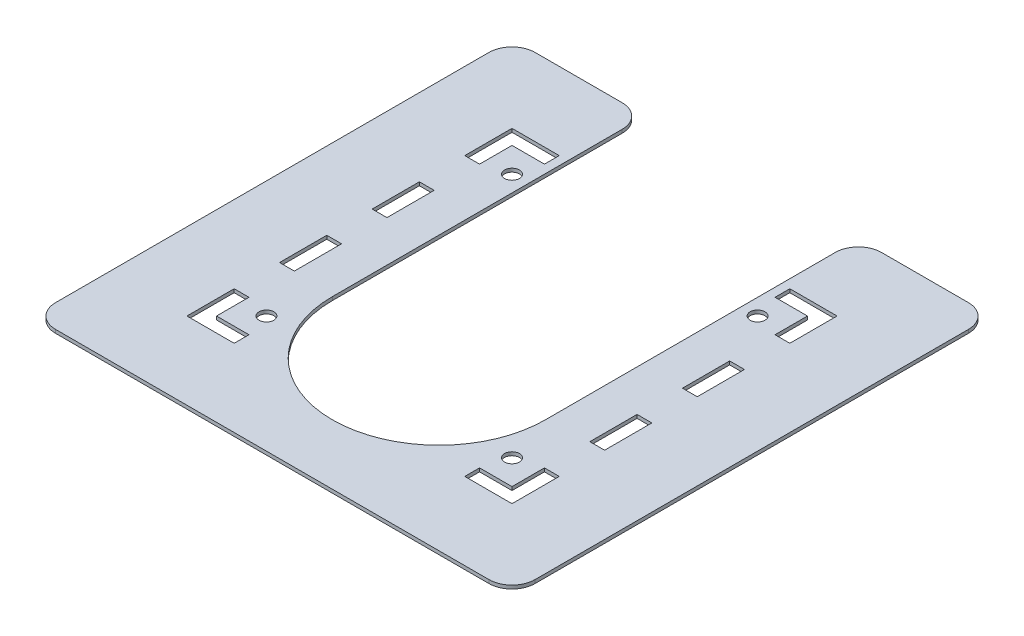
SolidWorks part; units mm, degrees
ref_plane "Front Plane" through (0, 0, 0) normal (0, 0, 1) x (1, 0, 0)
ref_plane "Top Plane" through (0, 0, 0) normal (0, 1, 0) x (1, 0, 0)
ref_plane "Right Plane" through (0, 0, 0) normal (1, 0, 0) x (0, 0, -1)
sketch "Sketch1" plane through (0, 0, 0) normal (0, 1, 0) x (1, 0, 0)
  line L0 (0, 0) -> (0, 21) construction
  line L1 (51.8722, -39.9014) -> (51.8722, 63.843) construction
  line L3 (51.8722, 63.843) -> (-51.8722, 63.843) construction
  line L4 (-51.8722, 63.843) -> (-51.8722, -39.9014) construction
  line L5 (51.8722, -34.9014) -> (51.8722, 58.843)
  line L6 (-46.8722, -39.9014) -> (46.8722, -39.9014)
  line L7 (51.8722, 63.843) -> (-51.8722, 63.843) construction
  line L8 (-51.8722, 58.843) -> (-51.8722, -34.9014)
  line L10 (36.8722, -39.9014) -> (36.8722, 63.843) construction
  line L11 (-36.8722, -39.9014) -> (-36.8722, 63.843) construction
  line L12 (36.8722, -39.9014) -> (36.8722, 63.843) construction
  line L13 (-36.8722, -39.9014) -> (-36.8722, 63.843) construction
  line L14 (23.0585, -3.843) -> (23.0585, 58.843)
  line L15 (-23.0585, -3.843) -> (-23.0585, 58.843)
  line L16 (-46.8722, 63.843) -> (-28.0585, 63.843)
  line L17 (28.0585, 63.843) -> (46.8722, 63.843)
  circle A0 centre (0, 0) radius 21 construction
  circle A1 centre (0, 0) radius 21 construction
  circle A2 centre (26.5585, -14.5877) radius 1.6 construction
  circle A3 centre (-26.5585, -14.5877) radius 1.6 construction
  circle A4 centre (26.5585, 38.5292) radius 1.6 construction
  circle A5 centre (-26.5585, 38.5292) radius 1.6 construction
  circle A6 centre (26.5585, -14.5877) radius 1.6
  circle A7 centre (-26.5585, -14.5877) radius 1.6
  circle A8 centre (26.5585, 38.5292) radius 1.6
  circle A9 centre (-26.5585, 38.5292) radius 1.6
  circle A10 centre (0, -3.843) radius 21.0585 construction
  arc A11 (-21.0585, -3.843) -> (21.0585, -3.843) centre (0, -3.843) ccw construction
  arc A12 (-23.0585, -3.843) -> (23.0585, -3.843) centre (0, -3.843) ccw
  arc A13 (28.0585, 63.843) -> (23.0585, 58.843) centre (28.0585, 58.843) ccw
  circle A14 centre (0, -3.843) radius 23.0585 construction
  arc A15 (-28.0585, 63.843) -> (-23.0585, 58.843) centre (-28.0585, 58.843) cw
  arc A16 (46.8722, 63.843) -> (51.8722, 58.843) centre (46.8722, 58.843) cw
  arc A17 (51.8722, -34.9014) -> (46.8722, -39.9014) centre (46.8722, -34.9014) cw
  arc A18 (-46.8722, -39.9014) -> (-51.8722, -34.9014) centre (-46.8722, -34.9014) cw
  arc A19 (-51.8722, 58.843) -> (-46.8722, 63.843) centre (-46.8722, 58.843) cw
  point P39 (31.0585, -3.843)
  point P42 (23.0585, 63.843)
  point P45 (-23.0585, 63.843)
  dimension "D1" = 2
  dimension "D2" = 5
sketch "Sketch2" plane through (0, 0, 0) normal (0, 0, 1) x (1, 0, 0)
  line L1 (51.8722, -0.75) -> (-51.8722, -0.75)
  line L2 (51.8722, -0.75) -> (51.8722, 0)
  line L3 (51.8722, 0) -> (-51.8722, 0)
  line L4 (-51.8722, -0.75) -> (-51.8722, 0)
extrude "Boss-Extrude1" add sketch "Sketch1" against normal up to vertex (0.75 mm away) up to point (51.8722, -0.75, 0)
sketch "Sketch3" plane through (0, 0, 0) normal (0, 1, 0) x (1, 0, 0)
  line L4 (31.9585, -3.1543) -> (35.1585, -3.1543)
  line L5 (31.9585, 7.0624) -> (31.9585, -3.1543)
  line L6 (35.1585, 7.0624) -> (31.9585, 7.0624)
  line L7 (35.1585, -3.1543) -> (35.1585, 7.0624)
  line L8 (31.9585, -3.1543) -> (35.1585, -3.1543)
  line L9 (31.9585, 7.0624) -> (31.9585, -3.1543)
  line L10 (35.1585, 7.0624) -> (31.9585, 7.0624)
  line L11 (35.1585, -3.1543) -> (35.1585, 7.0624)
  line L12 (35.1585, 16.8791) -> (35.1585, 27.0958)
  line L13 (31.9585, 16.8791) -> (35.1585, 16.8791)
  line L14 (35.1585, 36.9125) -> (35.1585, 47.1292)
  line L15 (35.1585, 47.1292) -> (24.9418, 47.1292)
  line L16 (24.9418, 47.1292) -> (24.9418, 43.9292)
  line L17 (24.9418, 43.9292) -> (31.9585, 43.9292)
  line L18 (31.9585, 43.9292) -> (31.9585, 36.9125)
  line L19 (31.9585, 36.9125) -> (35.1585, 36.9125)
  line L20 (35.1585, 36.9125) -> (35.1585, 47.1292)
  line L21 (35.1585, 47.1292) -> (24.9418, 47.1292)
  line L22 (24.9418, 47.1292) -> (24.9418, 43.9292)
  line L23 (24.9418, 43.9292) -> (31.9585, 43.9292)
  line L24 (31.9585, 43.9292) -> (31.9585, 36.9125)
  line L25 (31.9585, 36.9125) -> (35.1585, 36.9125)
  line L26 (31.9585, 27.0958) -> (31.9585, 16.8791)
  line L27 (35.1585, 27.0958) -> (31.9585, 27.0958)
  line L28 (35.1585, 16.8791) -> (35.1585, 27.0958)
  line L29 (31.9585, 16.8791) -> (35.1585, 16.8791)
  line L30 (31.9585, 27.0958) -> (31.9585, 16.8791)
  line L31 (35.1585, 27.0958) -> (31.9585, 27.0958)
  line L32 (-35.1585, 27.0958) -> (-35.1585, 16.8791)
  line L33 (-35.1585, 16.8791) -> (-31.9585, 16.8791)
  line L34 (-31.9585, 16.8791) -> (-31.9585, 27.0958)
  line L35 (-31.9585, 27.0958) -> (-35.1585, 27.0958)
  line L36 (-35.1585, 27.0958) -> (-35.1585, 16.8791)
  line L37 (-35.1585, 16.8791) -> (-31.9585, 16.8791)
  line L38 (-31.9585, 16.8791) -> (-31.9585, 27.0958)
  line L39 (-31.9585, 27.0958) -> (-35.1585, 27.0958)
  line L40 (-31.9585, 7.0624) -> (-35.1585, 7.0624)
  line L41 (-35.1585, 7.0624) -> (-35.1585, -3.1543)
  line L42 (-31.9585, 36.9125) -> (-31.9585, 43.9292)
  line L43 (-35.1585, 36.9125) -> (-31.9585, 36.9125)
  line L44 (-35.1585, 47.1292) -> (-35.1585, 36.9125)
  line L45 (-24.9418, 47.1292) -> (-35.1585, 47.1292)
  line L46 (-24.9418, 43.9292) -> (-24.9418, 47.1292)
  line L47 (-31.9585, 43.9292) -> (-24.9418, 43.9292)
  line L48 (-31.9585, 36.9125) -> (-31.9585, 43.9292)
  line L49 (-35.1585, 36.9125) -> (-31.9585, 36.9125)
  line L50 (-35.1585, 47.1292) -> (-35.1585, 36.9125)
  line L51 (-24.9418, 47.1292) -> (-35.1585, 47.1292)
  line L52 (-24.9418, 43.9292) -> (-24.9418, 47.1292)
  line L53 (-31.9585, 43.9292) -> (-24.9418, 43.9292)
  line L54 (31.9585, -12.971) -> (31.9585, -19.9877)
  line L55 (35.1585, -12.971) -> (31.9585, -12.971)
  line L56 (35.1585, -23.1877) -> (35.1585, -12.971)
  line L57 (24.9418, -23.1877) -> (35.1585, -23.1877)
  line L58 (24.9418, -19.9877) -> (24.9418, -23.1877)
  line L59 (31.9585, -19.9877) -> (24.9418, -19.9877)
  line L60 (31.9585, -12.971) -> (31.9585, -19.9877)
  line L61 (35.1585, -12.971) -> (31.9585, -12.971)
  line L62 (35.1585, -23.1877) -> (35.1585, -12.971)
  line L63 (24.9418, -23.1877) -> (35.1585, -23.1877)
  line L64 (24.9418, -19.9877) -> (24.9418, -23.1877)
  line L65 (31.9585, -19.9877) -> (24.9418, -19.9877)
  line L66 (-35.1585, -12.971) -> (-35.1585, -23.1877)
  line L67 (-35.1585, -23.1877) -> (-24.9418, -23.1877)
  line L68 (-24.9418, -23.1877) -> (-24.9418, -19.9877)
  line L69 (-24.9418, -19.9877) -> (-31.9585, -19.9877)
  line L70 (-31.9585, -19.9877) -> (-31.9585, -12.971)
  line L71 (-31.9585, -12.971) -> (-35.1585, -12.971)
  line L72 (-35.1585, -12.971) -> (-35.1585, -23.1877)
  line L73 (-35.1585, -23.1877) -> (-24.9418, -23.1877)
  line L74 (-24.9418, -23.1877) -> (-24.9418, -19.9877)
  line L75 (-24.9418, -19.9877) -> (-31.9585, -19.9877)
  line L76 (-31.9585, -19.9877) -> (-31.9585, -12.971)
  line L77 (-31.9585, -12.971) -> (-35.1585, -12.971)
  line L78 (-35.1585, -3.1543) -> (-31.9585, -3.1543)
  line L79 (-31.9585, -3.1543) -> (-31.9585, 7.0624)
  line L80 (-31.9585, 7.0624) -> (-35.1585, 7.0624)
  line L81 (-35.1585, 7.0624) -> (-35.1585, -3.1543)
  line L82 (-35.1585, -3.1543) -> (-31.9585, -3.1543)
  line L83 (-31.9585, -3.1543) -> (-31.9585, 7.0624)
  dimension "D1" = 0
  dimension "D2" = 0
  dimension "D3" = 0
  dimension "D4" = 0
  dimension "D5" = 0
  dimension "D6" = 0
  dimension "D7" = 0
  dimension "D8" = 0
extrude "Cut-Extrude1" cut sketch "Sketch3" against normal through all
sketch "Sketch4" [suppressed] plane through (0, 0, 0) normal (0, 1, 0) x (1, 0, 0)
  line L4 (15.0452, -40.0014) -> (15.0452, -36.8014)
  line L5 (15.0452, -36.8014) -> (4.8817, -36.8014)
  line L6 (4.8817, -36.8014) -> (4.8817, -40.0014)
  line L7 (4.8817, -40.0014) -> (15.0452, -40.0014)
  line L8 (15.0452, -40.0014) -> (15.0452, -36.8014)
  line L9 (15.0452, -36.8014) -> (4.8817, -36.8014)
  line L10 (4.8817, -36.8014) -> (4.8817, -40.0014)
  line L11 (4.8817, -40.0014) -> (15.0452, -40.0014)
  line L12 (-24.8087, -36.8014) -> (-34.9722, -36.8014)
  line L13 (-34.9722, -36.8014) -> (-34.9722, -40.0014)
  line L14 (-34.9722, -40.0014) -> (-24.8087, -40.0014)
  line L15 (-24.8087, -40.0014) -> (-24.8087, -36.8014)
  line L16 (-24.8087, -36.8014) -> (-34.9722, -36.8014)
  line L17 (-34.9722, -36.8014) -> (-34.9722, -40.0014)
  line L18 (-34.9722, -40.0014) -> (-24.8087, -40.0014)
  line L19 (-24.8087, -40.0014) -> (-24.8087, -36.8014)
  line L20 (24.8087, -36.8014) -> (24.8087, -40.0014)
  line L21 (24.8087, -40.0014) -> (34.9722, -40.0014)
  line L22 (34.9722, -40.0014) -> (34.9722, -36.8014)
  line L23 (34.9722, -36.8014) -> (24.8087, -36.8014)
  line L24 (24.8087, -36.8014) -> (24.8087, -40.0014)
  line L25 (24.8087, -40.0014) -> (34.9722, -40.0014)
  line L26 (34.9722, -40.0014) -> (34.9722, -36.8014)
  line L27 (34.9722, -36.8014) -> (24.8087, -36.8014)
  line L28 (34.9722, -24.8014) -> (31.7722, -24.8014)
  line L29 (31.7722, -24.8014) -> (31.7722, -30.0014)
  line L30 (34.9722, 41.743) -> (34.9722, 46.943)
  line L31 (34.9722, 46.943) -> (26.7722, 46.943)
  line L32 (26.7722, 46.943) -> (26.7722, 43.743)
  line L33 (26.7722, 43.743) -> (31.7722, 43.743)
  line L34 (31.7722, 43.743) -> (31.7722, 41.743)
  line L35 (31.7722, 41.743) -> (34.9722, 41.743)
  line L36 (34.9722, 41.743) -> (34.9722, 46.943)
  line L37 (34.9722, 46.943) -> (26.7722, 46.943)
  line L38 (26.7722, 46.943) -> (26.7722, 43.743)
  line L39 (26.7722, 43.743) -> (31.7722, 43.743)
  line L40 (31.7722, 43.743) -> (31.7722, 41.743)
  line L41 (31.7722, 41.743) -> (34.9722, 41.743)
  line L42 (31.7722, -30.0014) -> (34.9722, -30.0014)
  line L43 (34.9722, -30.0014) -> (34.9722, -24.8014)
  line L44 (34.9722, -24.8014) -> (31.7722, -24.8014)
  line L45 (31.7722, -24.8014) -> (31.7722, -30.0014)
  line L46 (31.7722, -30.0014) -> (34.9722, -30.0014)
  line L47 (34.9722, -30.0014) -> (34.9722, -24.8014)
  line L48 (-34.9722, 43.743) -> (-26.7722, 43.743)
  line L49 (-26.7722, 43.743) -> (-26.7722, 46.943)
  line L50 (-26.7722, 46.943) -> (-34.9722, 46.943)
  line L51 (-34.9722, 46.943) -> (-34.9722, 43.743)
  line L52 (-34.9722, 43.743) -> (-26.7722, 43.743)
  line L53 (-26.7722, 43.743) -> (-26.7722, 46.943)
  line L54 (-26.7722, 46.943) -> (-34.9722, 46.943)
  line L55 (-34.9722, 46.943) -> (-34.9722, 43.743)
  line L56 (-4.8817, -36.8014) -> (-15.0452, -36.8014)
  line L57 (-4.8817, -40.0014) -> (-4.8817, -36.8014)
  line L58 (-15.0452, -40.0014) -> (-4.8817, -40.0014)
  line L59 (-15.0452, -36.8014) -> (-15.0452, -40.0014)
  line L60 (-4.8817, -36.8014) -> (-15.0452, -36.8014)
  line L61 (-4.8817, -40.0014) -> (-4.8817, -36.8014)
  line L62 (-15.0452, -40.0014) -> (-4.8817, -40.0014)
  line L63 (-15.0452, -36.8014) -> (-15.0452, -40.0014)
  line L408 (16.7722, -24.8014) -> (16.7722, -30.0014) construction
  line L409 (19.9722, -30.0014) -> (16.7722, -30.0014) construction
  line L410 (19.9722, -24.8014) -> (19.9722, -30.0014) construction
  line L411 (19.9722, -24.8014) -> (16.7722, -24.8014) construction
  line L412 (16.7722, -24.8014) -> (16.7722, -30.0014)
  line L413 (19.9722, -30.0014) -> (16.7722, -30.0014)
  line L414 (19.9722, -24.8014) -> (19.9722, -30.0014)
  line L415 (19.9722, -24.8014) -> (16.7722, -24.8014)
  dimension "D1" = 0
  dimension "D2" = 0
  dimension "D3" = 0
  dimension "D4" = 0
  dimension "D5" = 0
  dimension "D6" = 0
  dimension "D7" = 0
extrude "Cut-Extrude2" [suppressed] cut sketch "Sketch4" against normal through all
